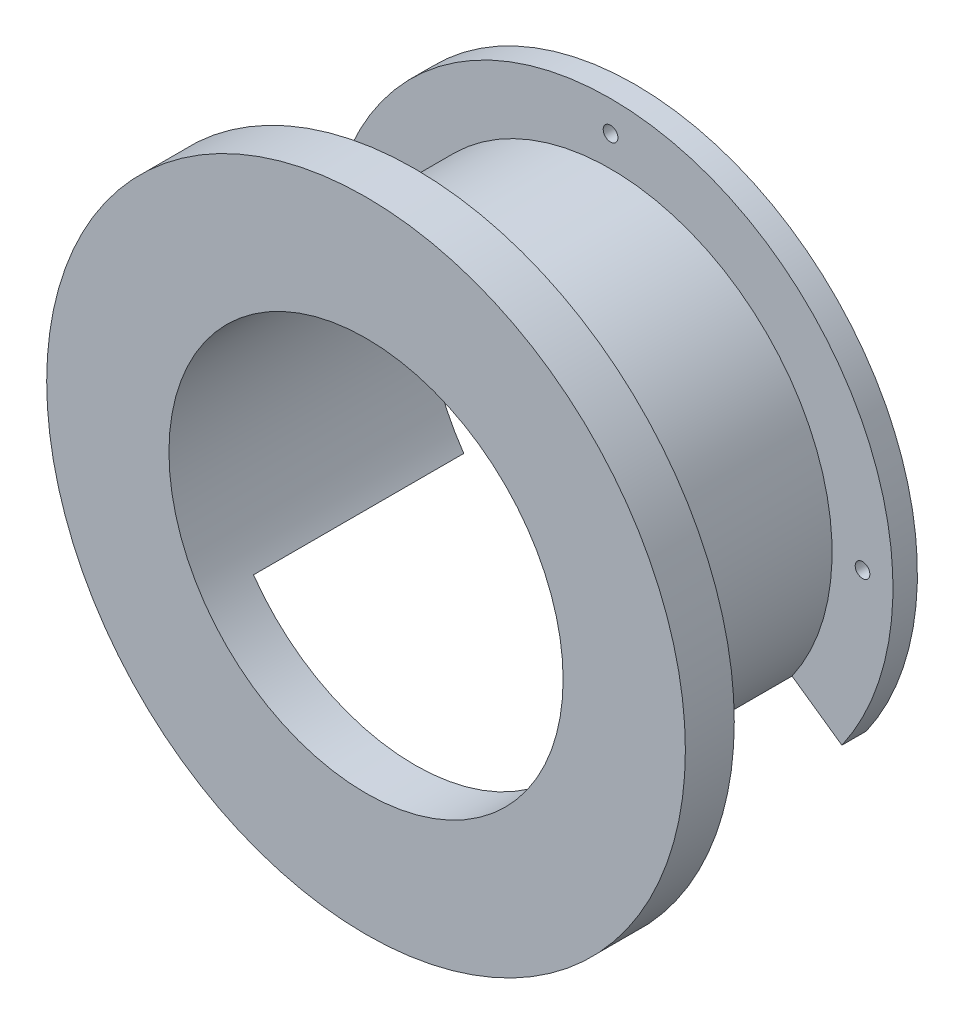
SolidWorks part; units mm, degrees
ref_plane "Front Plane" through (0, 0, 0) normal (0, 0, 1) x (1, 0, 0)
ref_plane "Top Plane" through (0, 0, 0) normal (0, 1, 0) x (1, 0, 0)
ref_plane "Right Plane" through (0, 0, 0) normal (1, 0, 0) x (0, 0, -1)
sketch "Sketch1" plane through (0, 0, 0) normal (0, 0, 1) x (1, 0, 0)
  line L0 (-94.6121, -66.2481) -> (-74.2152, -51.966)
  line L1 (94.6121, -66.2481) -> (74.2152, -51.966)
  line L2 (0, -173.8443) -> (0, 173.8443) construction
  circle A0 centre (0, 0) radius 115.5 construction
  arc A1 (94.6121, -66.2481) -> (-94.6121, -66.2481) centre (0, 0) ccw
  circle A2 centre (0, 0) radius 90.6 construction
  arc A3 (74.2152, -51.966) -> (-74.2152, -51.966) centre (0, 0) ccw
  point P10 (0, 0)
  dimension "baseStandOpeningAngle" = 55
extrude "Boss-Extrude1" add sketch "Sketch1" along normal blind 10
sketch "Sketch2" plane through (0, 0, 10) normal (0, 0, 1) x (1, 0, 0)
  line L2 (-66.0237, -46.2303) -> (-74.2152, -51.966)
  line L3 (66.0237, -46.2303) -> (74.2152, -51.966)
  arc A3 (74.2152, -51.966) -> (-74.2152, -51.966) centre (0, 0) ccw construction
  arc A4 (74.2152, -51.966) -> (-74.2152, -51.966) centre (0, 0) ccw
  arc A5 (66.0237, -46.2303) -> (-66.0237, -46.2303) centre (0, 0) ccw
  dimension "baseStandWallThickness" = 10
extrude "Boss-Extrude2" add sketch "Sketch2" along normal blind 100 and the other way offset from surface (6 mm away) 4 other way up to face at (0, 21.9715, 0)
sketch "Sketch3" plane through (0, 0, 110) normal (0, 0, 1) x (1, 0, 0)
  line L2 (-74.2152, -51.966) -> (-66.0237, -46.2303) construction
  line L3 (-74.2152, -51.966) -> (-66.0237, -46.2303)
  line L4 (66.0237, -46.2303) -> (74.2152, -51.966) construction
  line L5 (66.0237, -46.2303) -> (74.2152, -51.966)
  arc A0 (74.2152, -51.966) -> (-74.2152, -51.966) centre (0, 0) ccw construction
  arc A1 (74.2152, -51.966) -> (-74.2152, -51.966) centre (0, 0) ccw
  arc A4 (-106.9813, -74.9091) -> (106.9813, -74.9091) centre (0, 0) ccw
  arc A5 (106.9813, -74.9091) -> (-106.9813, -74.9091) centre (0, 0) ccw
  arc A6 (-74.2152, -51.966) -> (74.2152, -51.966) centre (0, 0) ccw construction
  arc A7 (-66.0237, -46.2303) -> (66.0237, -46.2303) centre (0, 0) ccw
  dimension "baseStandFootDiameterOffset" = 40
extrude "Boss-Extrude3" add sketch "Sketch3" against normal blind 20
sketch "mountingHoleLocations" plane through (0, 0, 10) normal (0, 0, 1) x (1, 0, 0)
  line L0 (90.6, 0) -> (-90.6, 0) construction
  line L1 (0, -90.6) -> (0, 90.6) construction
  line L2 (90.6, 0) -> (115.5, 0) construction
  line L3 (-90.6, 0) -> (-115.5, 0) construction
  line L4 (0, 90.6) -> (0, 115.5) construction
  arc A0 (94.6121, -66.2481) -> (-94.6121, -66.2481) centre (0, 0) ccw construction
  arc A2 (74.2152, -51.966) -> (-74.2152, -51.966) centre (0, 0) ccw construction
  point P3 (0, 0)
  point P4 (0, 0)
  point P7 (103.05, 0)
  point P12 (0, 103.05)
  point P13 (-103.05, 0)
hole_wizard "Ø6.0mm Dowel Hole4" positions "Sketch5" profile "Sketch6" hole size "Ø6.0" standard "ANSI Metric"
sketch "Sketch5" plane through (0, 0, 10) normal (0, 0, 1) x (1, 0, 0)
  point P0 (-103.05, 0)
  point P3 (103.05, 0)
  point P6 (0, 103.05)
sketch "Sketch6" plane through (-103.05, 0, 10) normal (1, 0, 0) x (0, -1, 0)
  line L0 (0, 0) -> (0, 10)
  line L1 (0, 10) -> (3, 10)
  line L2 (3, 10) -> (3, 0)
  line L3 (3, 0) -> (0, 0)
  line L4 (0, -6.35) -> (0, 107.95) construction
  dimension "Thru Hole Dia." = 6
  dimension "Thru Hole Depth" = 10
equation "\"generalFittingTolerance\"= 0.1mm'The general fitting tolerance between contacting parts"
equation "\"pelletWidth\"= 13mm'The Width of the pellet to be dispensed"
equation "\"pelletLength\"= 26mm'The length of the pellet to be dispensed"
equation "\"pelletThickness\"= 13mm'The Thickness of the pellet to be dispensed"
equation "\"pelletRadius\"= 10mm'The roundness / radius of the pellet to be dispensed"
equation "\"rotatingPlateDiameter\"= 100mm'the diameter of the rotating plate"
equation "\"rotatingPlateHeight\"= (\"pelletThickness\"*0.9)'The thickness of the rotating plate"
equation "\"rotatingPlateDiameterAllowance\"= 0.5mm'Allowance around the edge of the rotating plate"
equation "\"rotatingPlatePelletSlotLength\"= \"pelletLength\"*1.3'The length of the slot where a pellet will be captured"
equation "\"rotatingPlatePelletSlotWidth\"= \"pelletWidth\"*1.3'The width of the slot where a pellet will be captured"
equation "\"rotatingPlateNumberOfPelletSlots\"= ( (2*pi*(\"rotatingPlateDiameter\"/2)) / ((\"rotatingPlatePelletSlotLength\"*1.1)*3) )'The maximum number of pellet slots allows in the rotating plate for proper spacing"
equation "\"rotatingPlateAgitatorDiameter\"= ( \"rotatingPlateDiameter\"-((\"pelletWidth\"*1.3)*2.5) )'The diameter of the \"agitator\" section of the rotating plate"
equation "\"rotatingPlateAgitatorHeight\"= 80mm'The height of the \"agitator\" section of the rotating plate"
equation "\"rotatingPlateAgitatorTopRoundingRadius\"= 6mm'The rounding radius of the top of the \"agitator\" section of the rotating plate"
equation "\"rotatingPlateAgitatorBladeThickness\"= 4mm'The thickness of the blade on the \"agitator\" section of the rotating plate"
equation "\"rotatingPlateAgitatorBladeDistance\"= ( (\"rotatingPlateAgitatorDiameter\"+ 20mm) - (\"rotatingPlateAgitatorDiameter\") )'The distance offset of the blade from the surface of the \"agitator\" section of the rotating plate"
equation "\"rotatingPlateAgitatorBladeBottomGap\"= ( \"pelletThickness\"*1.2 )'The gap between the bottom of the blade and the base of the plate on the \"agitator\" section of the rotating plate"
equation "\"rotatingPlateAgitatorBladesNumber\"= ( 3 )'The number of blades on the \"agitator\" section of the rotating plate"
equation "\"hopperBaseInnerDiameter\"= (\"rotatingPlateDiameter\") + (\"rotatingPlateDiameterAllowance\"*2)'Diameter of the Base of the hopper where it meets the motor mount + rotating plate"
equation "\"hopperBaseOuterDiameter\"= (\"hopperBaseInnerDiameter\" + (\"hopperTankWallThickness\"*2) + 60mm)'Diameter of the Base of the hopper where it meets the motor mount + rotating plate"
equation "\"hopperBaseChamferAngle\"= 60deg'Angle of the chamfer of the Hopper base Toward the plate"
equation "\"hopperBaseLipOverhang\"= 5mm'The overhang amount of the hopper base lip"
equation "\"hopperBaseLipDepth\"= 5mm'The depth of the hopper base's overhang lip"
equation "\"hopperBaseLockNotchWidth\"= 10mm'The width of the hopper base \"lock\" notch to prevent rotation"
equation "\"hopperBaseLockNotchHeight\"= 10mm'The height of the hopper base \"lock\" notch to prevent rotation"
equation "\"hopperBaseRearNotchHeight\"= 8mm'The height of the rear snap-lock notch on the hopper base"
equation "\"hopperBaseRearNotchWidth\"= 8mm'The width of the rear snap-lock notch on the hopper base"
equation "\"hopperTankWallThickness\"= 5mm'The wall thickness of the hopper tank where pellet reserve will be stored"
equation "\"hopperTankDiameter\"= ( \"rotatingPlateDiameter\"*1.8 )'**Must be greater than \"rotatingPlateDiameter\" -- The inner diameter of the hopper tank where pellet reserve will be stored"
equation "\"hopperTankHeight\"= 200mm'The height of the hopper tank where pellet reserve will be stored"
equation "\"hopperTankCoverThickness\"= 10mm'The thickness of the Hopper Tank's cover"
equation "\"hopperTankCoverHandleLength\"= 60mm'The length of the handles on the hopper tank cover"
equation "\"hopperTankCoverHandleWidth\"= 20mm'The width of the handles on the hopper tank cover, defined as the offset from the cover's main edge"
equation "\"hopperBasePelletBlockerMountingSlotWidth\"= 5mm'The width of the pellet blocker mounting slot on the hopper base"
equation "\"hopperBasePelletBlockerMountingSlotOffsetFromTopOfChamfer\"= 15mm'The distance offset of the top of the pellet blocker mounting slot from the top of the hopper base chamfer"
equation "\"hopperBasePelletBlockerMountingSlotOffsetFromBottomOfChamfer\"= 10mm'The distance offset of the bottom of the pellet blocker mounting slot from the bottom of the hopper base chamfer"
equation "\"motorMountOffset\"= 30mm'The distance offset of the motor mount part from the hopper tank's outer edge"
equation "\"motorMountHeight\"= (\"motorHeight\" + \"motorFacePlateThickness\" + 0mm)'The height / thickness of the motor mount part"
equation "\"motorMountPelletThroughHoleLength\"= 40mm'The length of the pellet throughhole that routes through the motor mount and other parts"
equation "\"motorMountPelletThroughHoleWidth\"= 20mm'The width of the pellet throughhole that routes through the motor mount and other parts"
equation "\"motorDiameter\"= 35mm'The Diameter of the main motor unit"
equation "\"motorHeight\"= 13.4mm'The height of the main motor unit"
equation "\"motorConnectorWidth\"= 10mm'The width of the motor's electrical cable connector"
equation "\"motorConnectorLength\"= 8mm'The length of the motor's electrical cable connector"
equation "\"motorConnectorHeight\"= 5mm'The height of the motor's electrical cable connector"
equation "\"motorFacePlateLength\"= 50mm'The length of the motor faceplate"
equation "\"motorFacePlateWidth\"= 10mm'The width of the motor faceplate"
equation "\"motorFacePlateThickness\"= 1mm'The thickness of the motor faceplate"
equation "\"motorFacePlateCenterRadius\"= 20mm'The rounding radius of the motor faceplate center"
equation "\"motorFacePlateEndRadius\"= 10mm'The rounding radius of the motor faceplate ends"
equation "\"motorFacePlateMountingHoleDiameter\"= 6mm'The diameter of the motor faceplate's mounting holes"
equation "\"motorFacePlateMoutingHoleDistanceBetweenHoles\"= 42mm'The distance between the center of the mounting holes"
equation "\"motorSpindleDiameter\"= 2mm'The diameter of the motor spindle"
equation "\"motorSpindleFlatFaceLength\"= 1.5mm'The length of the flat face of the motor spindle"
equation "\"motorSpindleHeight\"= 9mm'The height of the motor spindle from the face of the motor"
equation "\"motorSpindleMountDiameter\"= 12mm'The diameter of the raised mount section of the motor where the spindle is attached"
equation "\"motorSpindleMountHeight\"= 1.5mm'The height of the raised mount section of the motor where the spindle is attached"
equation "\"irBeamUnitLength\"=20mm'The legth of the IR beam unit"
equation "\"irBeamUnitWidth\"=10mm'The width of the IR beam unit"
equation "\"irBeamUnitHeight\"=8mm'The height of the IR beam unit"
equation "\"irBeamUnitSlotWidth\"=2.03mm'The width of the slots on the outside of the IR beam unit"
equation "\"irBeamUnitSlotLength\"=5.10mm'The length of the slots of the outside of the IR beam unit"
equation "\"irBeamUnitSlotDepth\"=0.76mm'The depth of the slots on the outside of the IR beam unit"
equation "\"irBeamUnitSlotChamferAngle\"=45deg'The angle of the \"end\" of the slot on the outside of the IR beam unit"
equation "\"irBeamUnitSideSlotsDistanceFromBottom\"=3.98mm'The distance of the side slots on the outside of the IR beam unit from the bottom edge of the unit"
equation "\"irBeamUnitMountHoleDistanceFromBottom\"=5mm'The distance of the center mounting throughhole of the IR beam unit from the bottom edge of the unit"
equation "\"irBeamUnitMountHoleDiameter\"=2.40mm'The diameter of the center mounting throughhole of the IR beam unit"
equation "\"irBeamUnitMountHoleChamferDiameter\"=5.30mm'The diameter of the chamfer of the center mounting throughole of the IR beam unit"
equation "\"irBeamUnitMountHoleChamferDepth\"=2.65mm'The depth of the chamfer of the center mounting throughole of the IR beam unit"
equation "\"irBeamUnitLEDDistanceFromBottom\"=15mm'The distance of the center of the LED from the bottom edge of the IR beam unit"
equation "\"irBeamUnitLEDMountDiameter\"=8mm'The diameter of the LED mounting base of the IR beam unit"
equation "\"irBeamUnitLEDMountHeight\"=1.02mm'The height of the LED mounting base of the IR beam unit"
equation "\"irBeamUnitLEDDiameter\"=3.00mm'The diameter of the LED of the IR beam unit"
equation "\"irBeamUnitLEDFlatSectionHeight\"=0.65mm'The height of the \"flat\" section of the LED of the IR beam unit"
equation "\"irBeamUnitLEDDomeSectionDiameter\"=\"irBeamUnitLEDDiameter\"'The diameter of the \"domed\" section of the LED of the IR beam unit"
equation "\"irBeamUnitMountingPlateThickness\"=2mm'The thickness of the IR beam unit mounting plate"
equation "\"irBeamUnitMountingPlateAdjustmentSlotLength\"=10mm'The length of the variable/adjustable mounting slot of the IR beam unit mounting plate"
equation "\"pelletBlockerBaseWidth\"= (\"rotatingPlatePelletSlotWidth\"+\"rotatingPlateDiameterAllowance\")*1.1'The width of the base of the pellet blocker where it meets the rotating plate & pellet slot"
equation "\"pelletBlockerBaseLength\"= \"rotatingPlatePelletSlotLength\"*1.1'The length of the base of the pellet blocker where it meets the rotating plate & pellet slot"
equation "\"pelletBlockerBaseRoundingRadius\"= \"pelletWidth\"*0.5'The rounding radius of the base of the pellet blocker where it meets the rotating plate & pellet slot"
equation "\"pelletBlockerBaseHeight\"= \"rotatingPlateAgitatorBladeBottomGap\"*0.75'The height of the base of the pellet blocker where it meets the rotating plate & pellet slot"
equation "\"pelletBlockerNeckLength\"= 50mm'The length of the neck of the pellet blocker"
equation "\"pelletBlockerNeckTopRoundingRadius\"=2mm'The rounding radius of the top of the neck of the pellet blocker"
equation "\"pelletOutletTrackMountingPlateThickness\"= 2mm'The thickness of the Pellet Outlet Track Mounting Plate"
equation "\"pelletOutletTrackMountingPlateHingeHeight\"= (\"irBeamUnitWidth\" + \"irBeamUnitMountingPlateThickness\" + 2mm )'The height of the bottom of the hinge of the Pellet Outlet Mounting Plate"
equation "\"pelletOutletTrackMountingPlateHingeDiameter\"= 6mm'The inner diameter of the hinge on the Pellet Outlet Mounting Plate"
equation "\"pelletOutletTrackMountingPlateHingeOffsetFromHoleDistance\"= (\"pelletOutletTrackMountingPlateHingeDiameter\" + \"pelletOutletTrackMountingPlateThickness\" + 4mm)'The distance offset of the hinge of the Pellet Outlet Mounting Plate from the plate's mounting hole position"
equation "\"pelletOutletTrackHingeWidth\"= 10mm'The width of the pellet outlet track's hinge which mates with the hinge on the mounting plate"
equation "\"pelletOutletTrackHingeOffsetFromIRBeamUnitEdge\"= 6mm'The distance offset of the pelletOutletTrack's mating hinge from the edge of the IR Beam Unit"
equation "\"pelletOutletTrackEndingWidth\"= 50mm'The width of the pellet outlet Track at the end of the Track"
equation "\"pelletOutletTrackEndingLength\"= 30mm'The length of pellet outlet Track at the end of the Track"
equation "\"pelletOutletTrackWallHeight\"= 15mm'The height of the side walls of the pellet outlet Track"
equation "\"pelletOutletTrackThickness\"= 2mm'The thickness of the pellet outlet Track"
equation "\"baseStandMountingFaceHeight\"= 10mm'The height / thickness of the mounting face between the Base Stand and the Motor Mount parts"
equation "\"baseStandOpeningAngle\"= 55deg'The angle of the opening in the front of the Base Stand to allow for unobstructed pellet outlet"
equation "\"baseStandWallThickness\"= 10mm'The wall thickness of the Base Stand"
equation "\"baseStandHeight\"= 100mm'The overall height of the Base Stand part"
equation "\"baseStandFootDiameterOffset\"= 40mm'The distance offset of the Base Stand's foot ring"
equation "\"baseStandOpeningAngle@Sketch1\" = \"baseStandOpeningAngle\""
equation "\"D1@Boss-Extrude1\"=\"baseStandMountingFaceHeight\""
equation "\"baseStandWallThickness@Sketch2\" = \"baseStandWallThickness\""
equation "\"D2@Boss-Extrude2\"=\"irBeamUnitMountingPlateThickness\"*2"
equation "\"D1@Boss-Extrude2\"=\"baseStandHeight\""
equation "\"baseStandFootDiameterOffset@Sketch3\" = \"baseStandFootDiameterOffset\""
equation "\"baseStandFootHeight\"= 20mm'The height / thickness of the Base Stand's foot ring"
equation "\"D1@Boss-Extrude3\"=\"baseStandFootHeight\""
